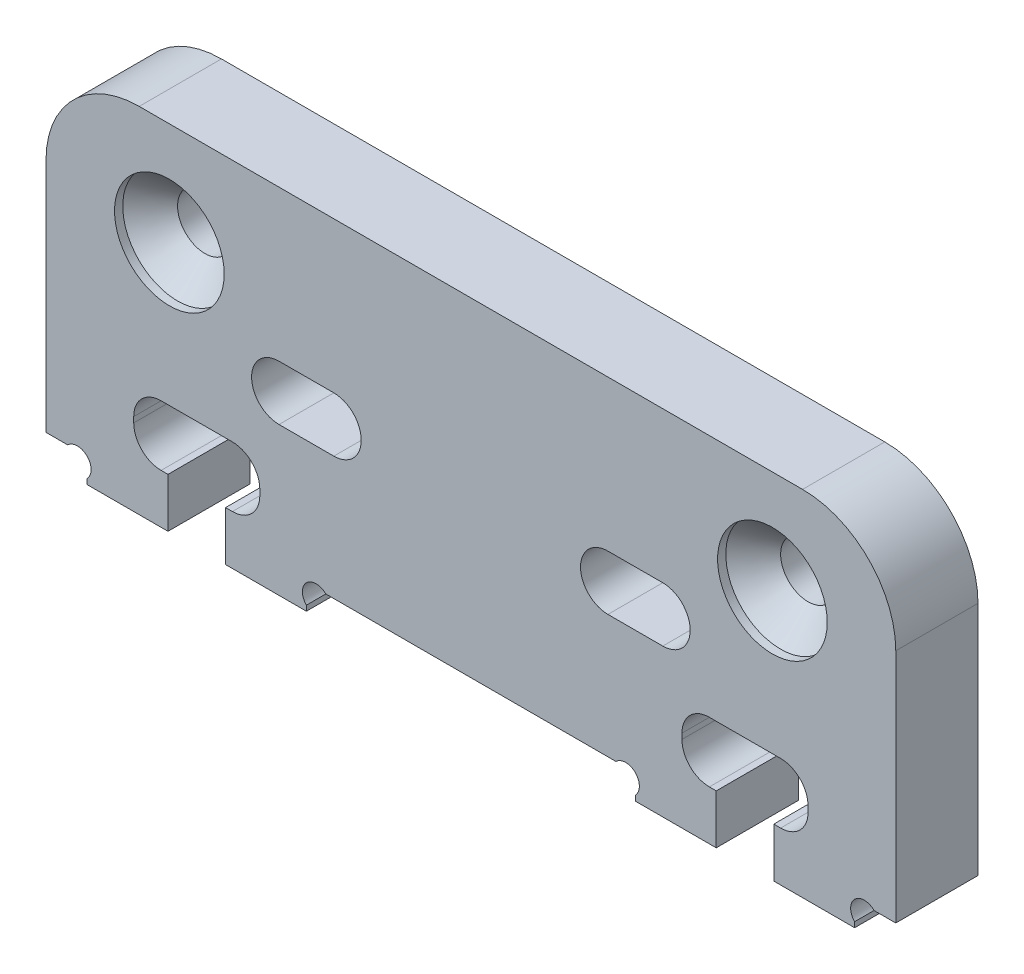
SolidWorks part; units mm, degrees
ref_plane "Front Plane" through (0, 0, 0) normal (0, 0, 1) x (1, 0, 0)
ref_plane "Top Plane" through (0, 0, 0) normal (0, 1, 0) x (1, 0, 0)
ref_plane "Right Plane" through (0, 0, 0) normal (1, 0, 0) x (0, 0, -1)
sketch "Sketch1" plane through (0, 0, 0) normal (0, 0, 1) x (1, 0, 0)
  line L0 (-10, -6.9) -> (-10, 6) construction
  line L1 (-15.5, 6) -> (15.5, 6)
  line L2 (-15.5, 6) -> (-15.5, -6)
  line L3 (-15.5, -6) -> (15.5, -6)
  line L4 (15.5, 6) -> (15.5, -6)
  line L5 (-15.5, 6) -> (15.5, -6) construction
  line L6 (-15.5, -6) -> (15.5, 6) construction
  line L7 (-15.5, -6) -> (-6, -6)
  line L9 (-14, -6.9) -> (-6, -6.9)
  line L10 (-6, -6) -> (-6, -6.9)
  line L11 (0, 6) -> (0, -6) construction
  line L12 (-11.05, -5.1) -> (-8.95, -5.1)
  line L13 (-11.05, -5.1) -> (-11.05, -6.9)
  line L14 (-11.05, -6.9) -> (-8.95, -6.9)
  line L15 (-8.95, -5.1) -> (-8.95, -6.9)
  line L16 (-11.05, -5.1) -> (-8.95, -6.9) construction
  line L17 (-11.05, -6.9) -> (-8.95, -5.1) construction
  line L18 (-12.3, -2.9) -> (-7.7, -2.9)
  line L19 (-12.3, -2.9) -> (-12.3, -5.1)
  line L20 (-12.3, -5.1) -> (-7.7, -5.1)
  line L21 (-7.7, -2.9) -> (-7.7, -5.1)
  line L22 (-12.3, -2.9) -> (-7.7, -5.1) construction
  line L23 (-12.3, -5.1) -> (-7.7, -2.9) construction
  line L24 (12.3, -2.9) -> (7.7, -2.9)
  line L25 (12.3, -2.9) -> (12.3, -5.1)
  line L26 (12.3, -5.1) -> (7.7, -5.1)
  line L27 (7.7, -2.9) -> (7.7, -5.1)
  line L28 (11.05, -5.1) -> (8.95, -5.1)
  line L29 (11.05, -5.1) -> (11.05, -6.9)
  line L30 (11.05, -6.9) -> (8.95, -6.9)
  line L31 (8.95, -5.1) -> (8.95, -6.9)
  line L32 (15.5, -6) -> (6, -6)
  line L33 (6, -6) -> (6, -6.9)
  line L34 (14, -6.9) -> (6, -6.9)
  line L36 (-14, -6.9) -> (-14, -6)
  line L37 (14, -6.9) -> (14, -6)
  line L38 (10, -2.9) -> (10, -6.9) construction
  line L39 (7, -0.5) -> (5, -0.5) construction
  line L40 (7, -1.5) -> (5, -1.5)
  line L41 (7, 0.5) -> (5, 0.5)
  line L42 (-7, -0.5) -> (-5, -0.5) construction
  line L43 (-7, -1.5) -> (-5, -1.5)
  line L44 (-7, 0.5) -> (-5, 0.5)
  arc A0 (7, -1.5) -> (7, 0.5) centre (7, -0.5) ccw
  arc A1 (5, 0.5) -> (5, -1.5) centre (5, -0.5) ccw
  arc A2 (-7, -1.5) -> (-7, 0.5) centre (-7, -0.5) cw
  arc A3 (-5, 0.5) -> (-5, -1.5) centre (-5, -0.5) cw
  point P0 (0, 0)
  point P11 (-10, -6)
  point P16 (-10, -4)
  point P40 (6, -0.5)
  point P47 (-6, -0.5)
  dimension "D1" = 31
  dimension "D2" = 12
  dimension "D3" = 0.9
  dimension "D4" = 8
  dimension "D5" = 2.1
  dimension "D6" = 1.8
  dimension "D7" = 2.2
  dimension "D8" = 4.6
  dimension "D9" = 20
  dimension "D10" = 2
  dimension "D11" = 2
  dimension "D12" = 12
  dimension "D13" = 5.5
extrude "Base shape" add sketch "Sketch1" along normal blind 3
fillet "Edge radiuses" radius 3.4 2 edges at (15.5, 6, 1.5) (-15.5, 6, 1.5)
sketch "Sketch3" plane through (0, 0, 3) normal (0, 0, -1) x (-1, 0, 0)
  line L0 (12.1, 6) -> (-12.1, 6) construction
  line L3 (0, 6) -> (0, -6) construction
  line L5 (6, -6) -> (-6, -6) construction
  circle A0 centre (-11, 2.25) radius 1
  circle A1 centre (11, 2.25) radius 1
  point P0 (0, 0)
  point P2 (-11, 2.25)
  dimension "D1" = 2
  dimension "D3" = 22
  dimension "D2" = 3.75
extrude "Camera mount holes" cut sketch "Sketch3" along normal up to next contours A0 | A1
hole_wizard "CSK for M2 Flat Head Machine Screw1" positions "Sketch4" profile "Sketch5" countersink size "M2" standard "ANSI Metric" end condition through all
sketch "Sketch4" plane through (0, 0, 3) normal (0, 0, 1) x (1, 0, 0)
  point P0 (-11, 2.25)
  point P3 (11, 2.25)
sketch "Sketch5" plane through (-11, 2.25, 3) normal (1, 0, 0) x (0, -1, 0)
  line L0 (0, 0) -> (0, 3)
  line L1 (0, 3) -> (1, 3)
  line L2 (1, 3) -> (1, 1.3)
  line L3 (1, 1.3) -> (2, 0.3)
  line L4 (2, 0.3) -> (2, 0)
  line L6 (2, 0) -> (0, 0)
  line L7 (-1, 1.3) -> (-2, 0.3) construction
  line L11 (0, -6.35) -> (0, 107.95) construction
  dimension "Thru Hole Dia." = 2
  dimension "Thru Hole Depth" = 3
  dimension "C'Sink Dia." = 4
  dimension "C'Sink Angle" = 90
  dimension "Head Clearance" = 0.3
fillet "Milling radiuses" radius 1 8 edges at (-7.7, -2.9, 1.5) (-7.7, -5.1, 1.5) (12.3, -5.1, 1.5) (12.3, -2.9, 1.5) (7.7, -2.9, 1.5) (7.7, -5.1, 1.5) (-12.3, -5.1, 1.5) (-12.3, -2.9, 1.5)
sketch "Sketch8" plane through (0, 0, 3) normal (0, 0, -1) x (-1, 0, 0)
  line L0 (-14, -6) -> (14, -6) construction
  line L1 (-14, -6) -> (-2, 6) construction
  line L2 (12.1, 6) -> (-12.1, 6) construction
  line L3 (0, 6) -> (0, -6) construction
  line L4 (-11.05, -6.9) -> (-8.95, -6.9) construction
  line L5 (-10, -6.9) -> (-10, -2.9) construction
  line L6 (-11.3, -2.9) -> (-8.7, -2.9) construction
  line L7 (-15.5, -6) -> (-14, -6) construction
  line L8 (-14, -6) -> (-14, -6.9) construction
  circle A0 centre (-14.3536, -6.3536) radius 0.5
  circle A1 centre (14.3536, -6.3536) radius 0.5
  circle A2 centre (-5.6464, -6.3536) radius 0.5
  circle A3 centre (5.6464, -6.3536) radius 0.5
  point P2 (-14, -6.9)
  dimension "D2" = 1
  dimension "D1" = 45
extrude "Milling cuts 1mm" cut sketch "Sketch8" along normal up to next
sketch "Milling sketch 1mm" plane through (0, 0, 3) normal (0, 0, 1) x (1, 0, 0)
  line L1 (-15.5, -6) -> (-14.7071, -6) construction
  line L2 (0, 6) -> (0, -6) construction
  line L3 (-15.5, -6) -> (-14.7071, -6)
  line L4 (-14, -6.7071) -> (-14, -7.5)
  line L5 (-14, -7.5) -> (-15.5, -7.5)
  line L6 (-15.5, -7.5) -> (-15.5, -6)
  line L7 (-6, -6.7071) -> (-6, -7.5)
  line L8 (-6, -7.5) -> (-4.5, -7.5)
  line L9 (-4.5, -7.5) -> (-4.5, -6)
  line L10 (-5.2929, -6) -> (5.2929, -6) construction
  line L11 (-4.5, -6) -> (-5.2929, -6)
  line L12 (-12.1, 6) -> (12.1, 6) construction
  line L13 (14, -6.7071) -> (14, -7.5)
  line L14 (15.5, -6) -> (14.7071, -6)
  line L15 (15.5, -7.5) -> (15.5, -6)
  line L16 (14, -7.5) -> (15.5, -7.5)
  line L17 (6, -6.7071) -> (6, -7.5)
  line L18 (4.5, -6) -> (5.2929, -6)
  line L19 (4.5, -7.5) -> (4.5, -6)
  line L20 (6, -7.5) -> (4.5, -7.5)
  arc A2 (-5.2929, -6) -> (-6, -6.7071) centre (-5.6464, -6.3536) ccw construction
  arc A3 (-14, -6.7071) -> (-14.7071, -6) centre (-14.3536, -6.3536) ccw construction
  arc A4 (14, -6.7071) -> (14.7071, -6) centre (14.3536, -6.3536) cw
  arc A5 (5.2929, -6) -> (6, -6.7071) centre (5.6464, -6.3536) cw
  arc A6 (-5.2929, -6) -> (-6, -6.7071) centre (-5.6464, -6.3536) ccw
  arc A7 (-14, -6.7071) -> (-14.7071, -6) centre (-14.3536, -6.3536) ccw
equation "\"D2@Sketch3\"=7.5/2"
